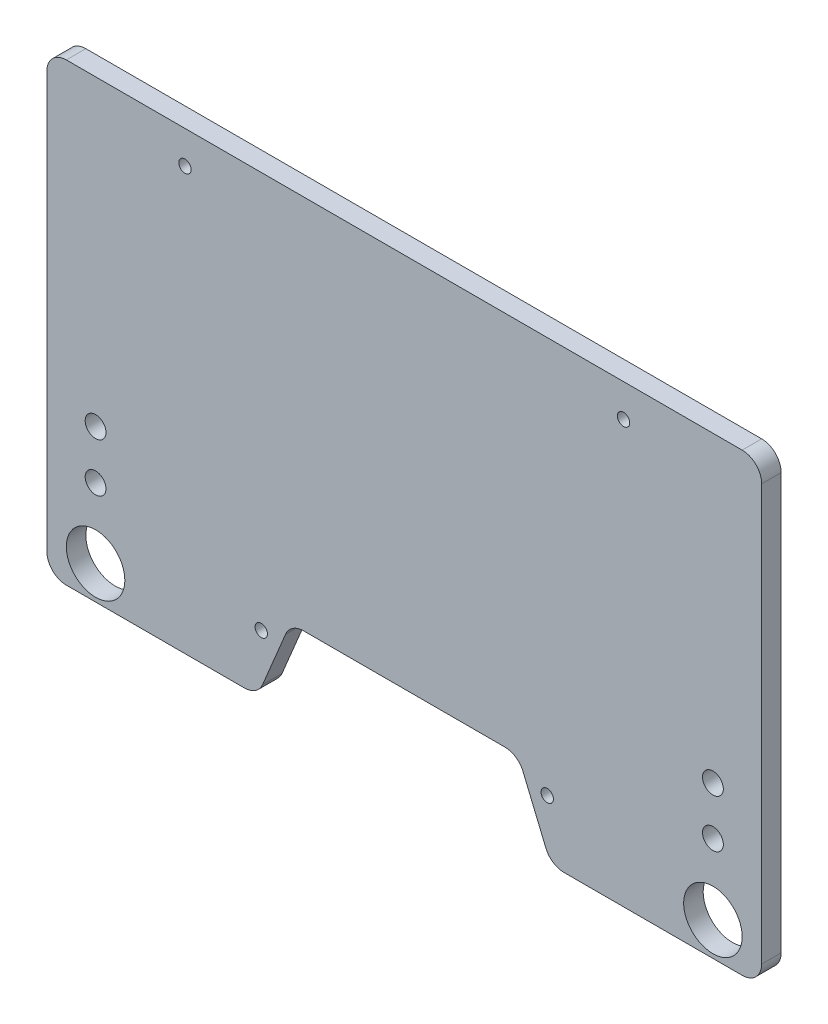
SolidWorks part; units mm, degrees
ref_plane "前视基准面" through (0, 0, 0) normal (0, 0, 1) x (1, 0, 0)
ref_plane "上视基准面" through (0, 0, 0) normal (0, 1, 0) x (1, 0, 0)
ref_plane "右视基准面" through (0, 0, 0) normal (1, 0, 0) x (0, 0, -1)
sketch "草图1" plane through (0, 0, 0) normal (0, 0, 1) x (1, 0, 0)
  line L0 (32, 23.2799) -> (63, 23.2799)
  line L1 (-4.5, 81.1154) -> (99.5, 81.1154)
  line L2 (-7.5, 78.1154) -> (-7.5, 14.1154)
  line L3 (-4.5, 11.1154) -> (22.9315, 11.1154)
  line L4 (102.5, 78.1154) -> (102.5, 14.1154)
  line L5 (90.5, 11.1154) -> (99.5, 11.1154) construction
  line L6 (102.5, 14.1154) -> (102.5, 28.65) construction
  line L7 (28.2692, 19.1261) -> (29.2308, 21.4338) construction
  line L9 (65.7692, 21.4338) -> (66.7308, 19.1261) construction
  line L10 (65.7692, 21.4338) -> (66.7308, 19.1261)
  line L11 (28.2692, 19.1261) -> (25.7007, 12.9616)
  line L12 (28.2692, 19.1261) -> (29.2308, 21.4338)
  line L14 (66.7308, 19.1261) -> (69.2993, 12.9616)
  line L15 (72.0685, 11.1154) -> (99.5, 11.1154)
  arc A0 (99.5, 81.1154) -> (102.5, 78.1154) centre (99.5, 78.1154) cw
  arc A1 (-4.5, 81.1154) -> (-7.5, 78.1154) centre (-4.5, 78.1154) ccw
  arc A2 (-7.5, 14.1154) -> (-4.5, 11.1154) centre (-4.5, 14.1154) ccw
  arc A3 (99.5, 11.1154) -> (102.5, 14.1154) centre (99.5, 14.1154) ccw
  circle A4 centre (0, 34.5) radius 1.6
  arc A5 (32, 23.2799) -> (29.2308, 21.4338) centre (32, 20.2799) ccw construction
  arc A6 (65.7692, 21.4338) -> (63, 23.2799) centre (63, 20.2799) ccw construction
  circle A7 centre (0, 27) radius 1.6
  arc A8 (69.2993, 12.9616) -> (72.0685, 11.1154) centre (72.0685, 14.1154) ccw
  arc A9 (25.7007, 12.9616) -> (22.9315, 11.1154) centre (22.9315, 14.1154) cw
  arc A10 (65.7692, 21.4338) -> (63, 23.2799) centre (63, 20.2799) ccw
  arc A11 (32, 23.2799) -> (29.2308, 21.4338) centre (32, 20.2799) ccw
  circle A12 centre (95, 34.5) radius 1.6
  circle A13 centre (95, 27.1) radius 1.6
  circle A14 centre (13.75, 76.0799) radius 0.95
  circle A15 centre (81.25, 76.0799) radius 0.95
  circle A16 centre (69.5, 20.0799) radius 0.95
  circle A17 centre (25.5, 20.0799) radius 0.95
  point P21 (70.0685, 11.1154)
  dimension "D2" = 3
  dimension "D3" = 3
  dimension "D4" = 3.2
  dimension "D5" = 1.9
  dimension "D1" = 70
extrude "凸台-拉伸1" add sketch "草图1" along normal blind 3
sketch "Sketch1" plane through (0, 0, 3) normal (0, 0, 1) x (1, 0, 0)
  circle A0 centre (0, 16.25) radius 4.5
  circle A1 centre (95, 16.25) radius 4.5
  dimension "D1" = 9
extrude "Cut-Extrude1" cut sketch "Sketch1" against normal blind 25
